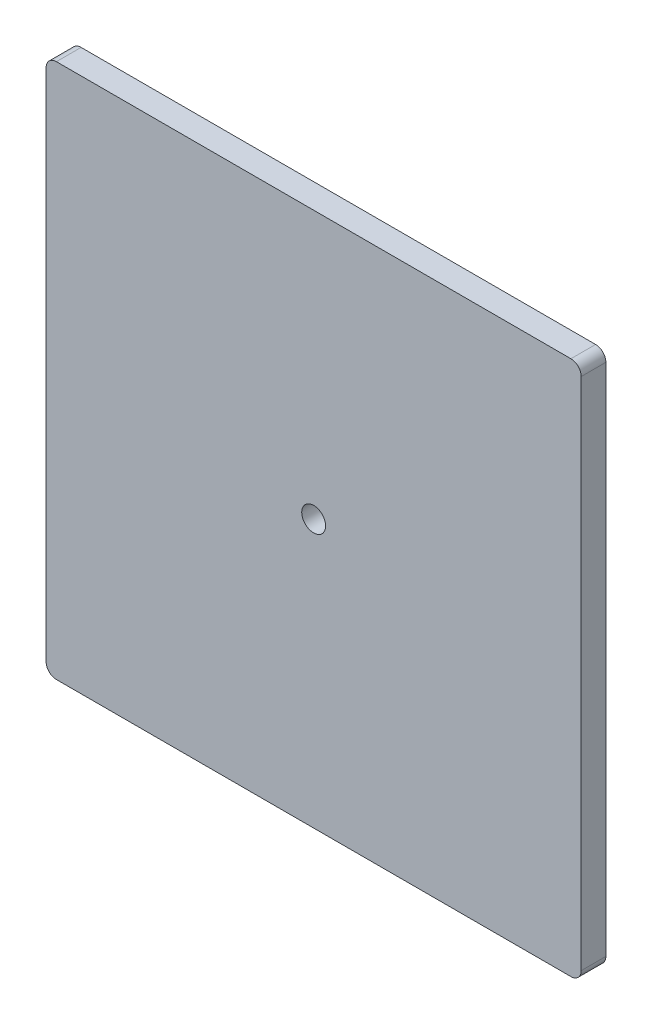
SolidWorks part; units mm, degrees
ref_plane "Front Plane" through (0, 0, 0) normal (0, 0, 1) x (1, 0, 0)
ref_plane "Top Plane" through (0, 0, 0) normal (0, 1, 0) x (1, 0, 0)
ref_plane "Right Plane" through (0, 0, 0) normal (1, 0, 0) x (0, 0, -1)
sketch "Sketch1" plane through (0, 0, 0) normal (0, 0, 1) x (1, 0, 0)
  line L1 (-125, 130) -> (125, 130)
  line L2 (-130, 125) -> (-130, -125)
  line L3 (-125, -130) -> (125, -130)
  line L4 (130, 125) -> (130, -125)
  line L5 (-130, 130) -> (130, -130) construction
  line L6 (-130, -130) -> (130, 130) construction
  arc A0 (-125, 130) -> (-130, 125) centre (-125, 125) ccw
  arc A1 (125, 130) -> (130, 125) centre (125, 125) cw
  arc A2 (-125, -130) -> (-130, -125) centre (-125, -125) cw
  arc A3 (125, -130) -> (130, -125) centre (125, -125) ccw
  point P0 (0, 0)
  dimension "D1" = 5
  dimension "D2" = 5
  dimension "D3" = 5
  dimension "D4" = 5
extrude "Boss-Extrude1" add sketch "Sketch1" along normal blind 12
sketch "Sketch2" plane through (0, 0, 12) normal (0, 0, 1) x (1, 0, 0)
  circle A0 centre (0, 0) radius 5.795
extrude "Cut-Extrude1" cut sketch "Sketch2" against normal blind 10
